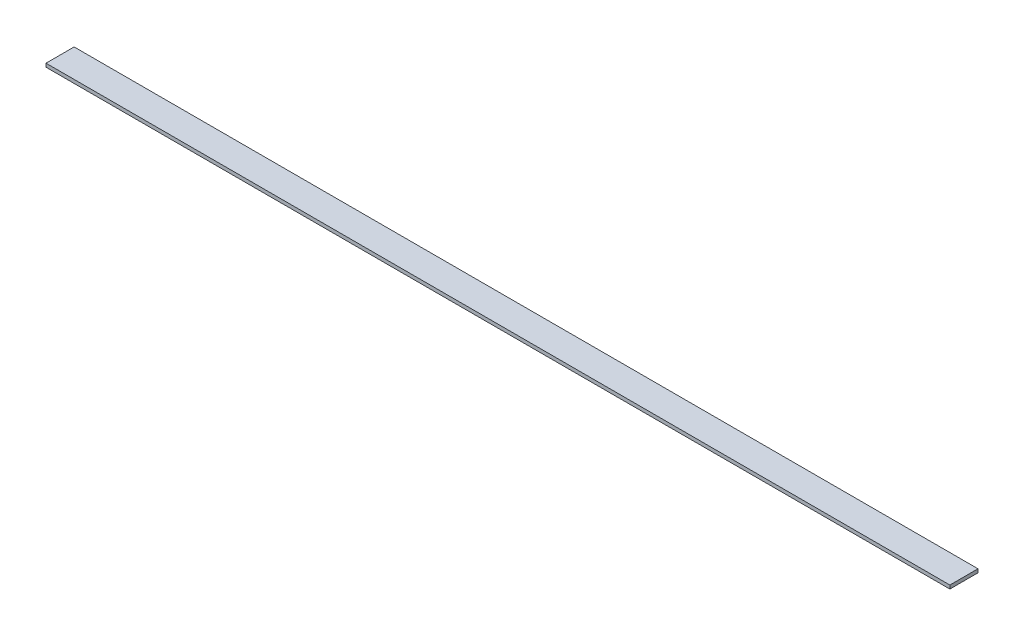
SolidWorks part; units mm, degrees
ref_plane "Front" through (0, 0, 0) normal (0, 0, 1) x (1, 0, 0)
ref_plane "Top" through (0, 0, 0) normal (0, 1, 0) x (1, 0, 0)
ref_plane "Right" through (0, 0, 0) normal (1, 0, 0) x (0, 0, -1)
sketch "Sketch2" plane through (0, 0, 0) normal (0, 1, 0) x (1, 0, 0)
  line L1 (0, 0) -> (1631.95, 0)
  line L2 (0, 0) -> (0, 50.8)
  line L3 (0, 50.8) -> (1631.95, 50.8)
  line L4 (1631.95, 0) -> (1631.95, 50.8)
  dimension "D1" = 50.8
  dimension "D2" = 1631.95
extrude "Boss-Extrude1" add sketch "Sketch2" along normal blind 6.35
